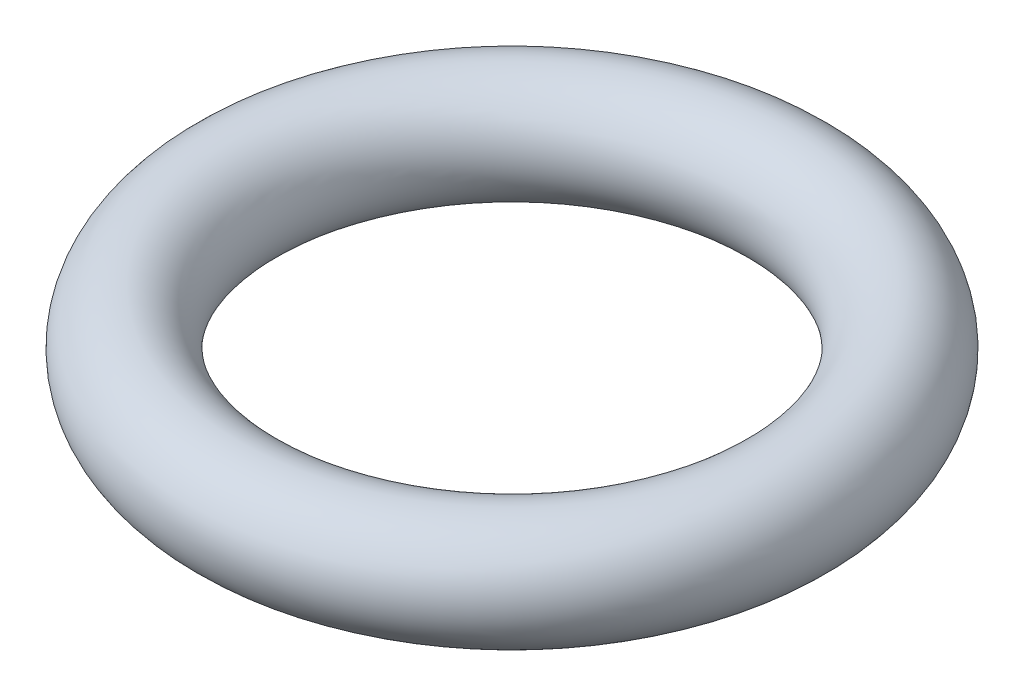
SolidWorks part; units mm, degrees
ref_plane "前视基准面" through (0, 0, 0) normal (0, 0, 1) x (1, 0, 0)
ref_plane "上视基准面" through (0, 0, 0) normal (0, 1, 0) x (1, 0, 0)
ref_plane "右视基准面" through (0, 0, 0) normal (1, 0, 0) x (0, 0, -1)
sketch "草图1" plane through (0, 0, 0) normal (0, 0, 1) x (1, 0, 0)
  line L0 (0, 0) -> (0, 7.6203) construction
  circle A0 centre (9.9524, 0) radius 2
  dimension "D1" = 4
  dimension "D2" = 9.9524
revolve "旋转1" add sketch "草图1" angle 360 about L0
